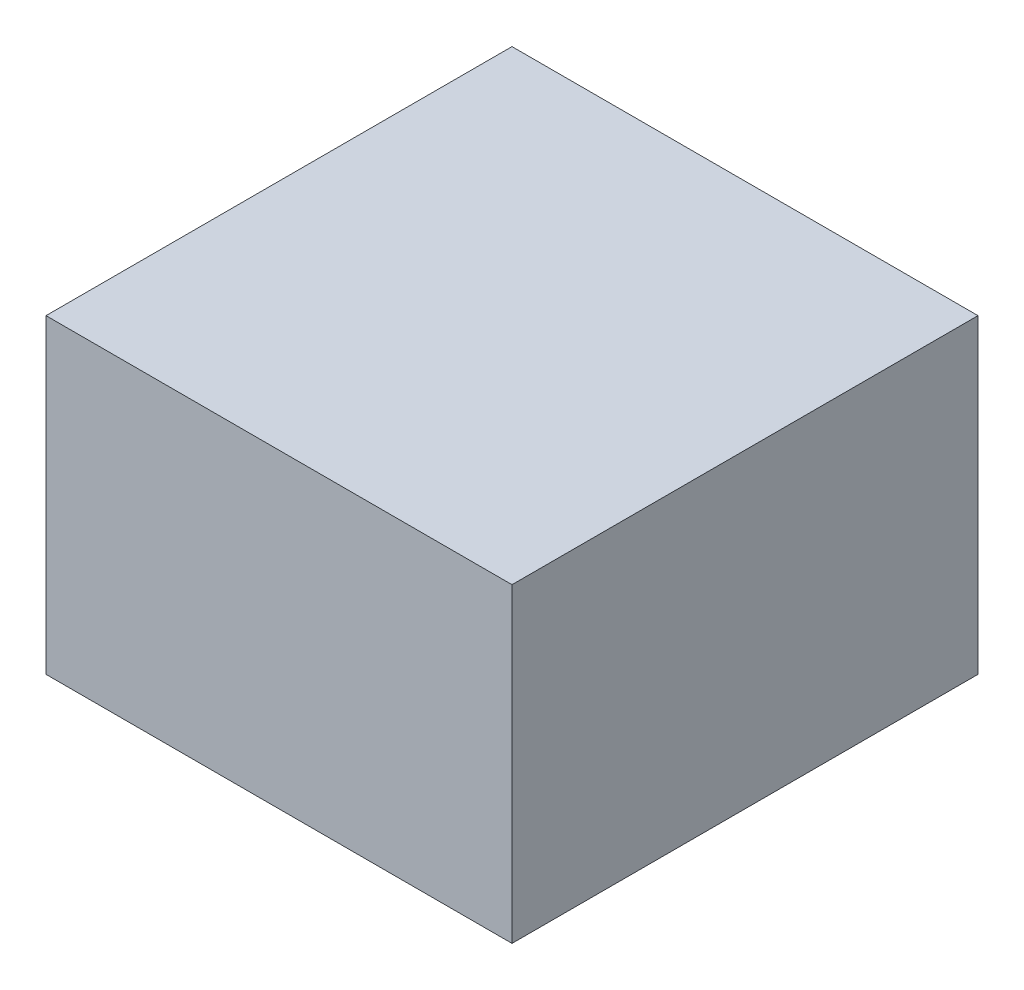
SolidWorks part; units mm, degrees
ref_plane "Front Plane" through (0, 0, 0) normal (0, 0, 1) x (1, 0, 0)
ref_plane "Top Plane" through (0, 0, 0) normal (0, 1, 0) x (1, 0, 0)
ref_plane "Right Plane" through (0, 0, 0) normal (1, 0, 0) x (0, 0, -1)
sketch "Sketch1" plane through (0, 0, 0) normal (0, 1, 0) x (1, 0, 0)
  line L1 (-76.2, -76.2) -> (76.2, -76.2)
  line L2 (-76.2, -76.2) -> (-76.2, 76.2)
  line L3 (-76.2, 76.2) -> (76.2, 76.2)
  line L4 (76.2, -76.2) -> (76.2, 76.2)
  line L5 (-76.2, -76.2) -> (76.2, 76.2) construction
  line L6 (-76.2, 76.2) -> (76.2, -76.2) construction
  point P0 (0, 0)
  dimension "D1" = 152.4
  dimension "D2" = 152.4
extrude "Extrude1" add sketch "Sketch1" along normal mid plane 101.6
